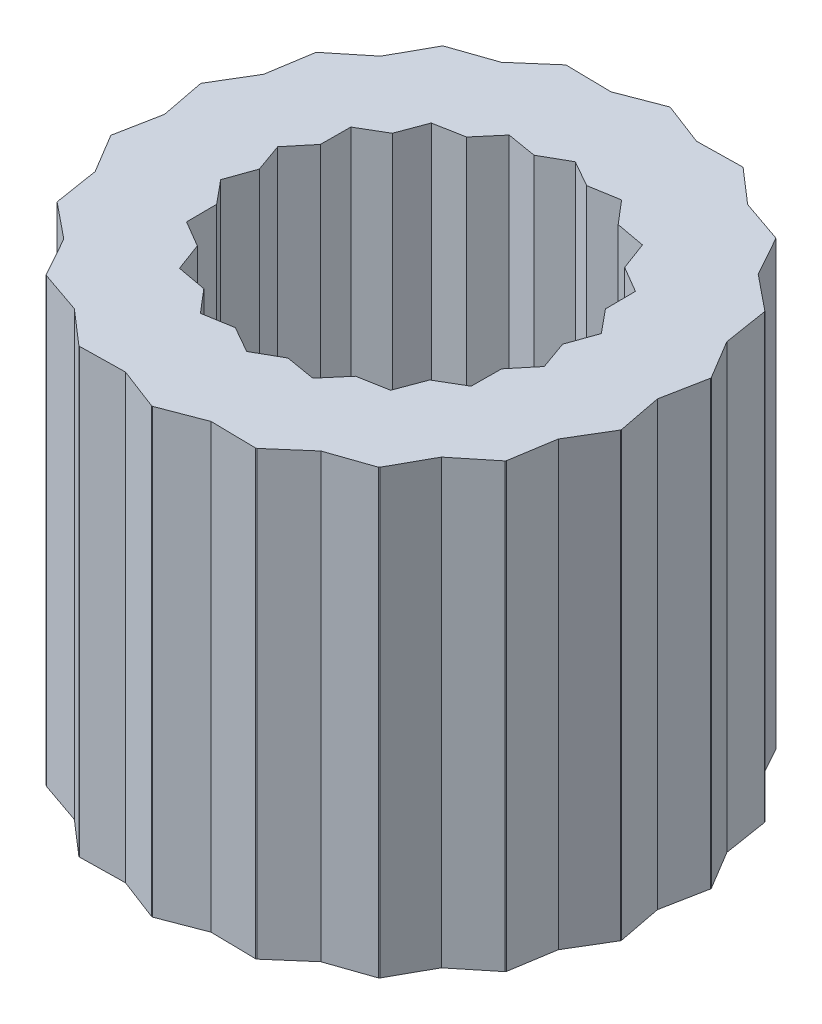
SolidWorks part; units mm, degrees
ref_plane "Front Plane" through (0, 0, 0) normal (0, 0, 1) x (1, 0, 0)
ref_plane "Top Plane" through (0, 0, 0) normal (0, 1, 0) x (1, 0, 0)
ref_plane "Right Plane" through (0, 0, 0) normal (1, 0, 0) x (0, 0, -1)
sketch "Sketch1" plane through (0, 0, 0) normal (0, 1, 0) x (1, 0, 0)
  line L0 (0, 0) -> (-0.8763, 4.97) construction
  line L1 (0, 0) -> (0.8632, 4.8954) construction
  line L2 (0, 0) -> (0, 4.9679) construction
  line L3 (0, 4.1) -> (-0.6772, 3.8408)
  line L4 (0, 4.1) -> (0.6772, 3.8408)
  line L5 (0, 2.6) -> (-0.4168, 2.3635)
  line L6 (0, 2.6) -> (0.4168, 2.3635)
  line L7 (1.4023, 3.8527) -> (0.6772, 3.8408)
  line L8 (1.4023, 3.8527) -> (1.95, 3.3775)
  line L9 (0.8893, 2.4432) -> (0.4168, 2.3635)
  line L10 (0.8893, 2.4432) -> (1.2, 2.0785)
  line L11 (2.6354, 3.1408) -> (1.95, 3.3775)
  line L12 (2.6354, 3.1408) -> (2.9876, 2.5069)
  line L13 (1.6712, 1.9917) -> (1.2, 2.0785)
  line L14 (1.6712, 1.9917) -> (1.8385, 1.5427)
  line L15 (3.5507, 2.05) -> (2.9876, 2.5069)
  line L16 (3.5507, 2.05) -> (3.6648, 1.3339)
  line L17 (2.2517, 1.3) -> (1.8385, 1.5427)
  line L18 (2.2517, 1.3) -> (2.2553, 0.8208)
  line L19 (4.0377, 0.712) -> (3.6648, 1.3339)
  line L20 (4.0377, 0.712) -> (3.9, 0)
  line L21 (2.5605, 0.4515) -> (2.2553, 0.8208)
  line L22 (2.5605, 0.4515) -> (2.4, 0)
  line L23 (4.0377, -0.712) -> (3.9, 0)
  line L24 (4.0377, -0.712) -> (3.6648, -1.3339)
  line L25 (2.5605, -0.4515) -> (2.4, 0)
  line L26 (2.5605, -0.4515) -> (2.2553, -0.8208)
  line L27 (3.5507, -2.05) -> (3.6648, -1.3339)
  line L28 (3.5507, -2.05) -> (2.9876, -2.5069)
  line L29 (2.2517, -1.3) -> (2.2553, -0.8208)
  line L30 (2.2517, -1.3) -> (1.8385, -1.5427)
  line L31 (2.6354, -3.1408) -> (2.9876, -2.5069)
  line L32 (2.6354, -3.1408) -> (1.95, -3.3775)
  line L33 (1.6712, -1.9917) -> (1.8385, -1.5427)
  line L34 (1.6712, -1.9917) -> (1.2, -2.0785)
  line L35 (1.4023, -3.8527) -> (1.95, -3.3775)
  line L36 (1.4023, -3.8527) -> (0.6772, -3.8408)
  line L37 (0.8893, -2.4432) -> (1.2, -2.0785)
  line L38 (0.8893, -2.4432) -> (0.4168, -2.3635)
  line L39 (0, -4.1) -> (0.6772, -3.8408)
  line L40 (0, -4.1) -> (-0.6772, -3.8408)
  line L41 (0, -2.6) -> (0.4168, -2.3635)
  line L42 (0, -2.6) -> (-0.4168, -2.3635)
  line L43 (-1.4023, -3.8527) -> (-0.6772, -3.8408)
  line L44 (-1.4023, -3.8527) -> (-1.95, -3.3775)
  line L45 (-0.8893, -2.4432) -> (-0.4168, -2.3635)
  line L46 (-0.8893, -2.4432) -> (-1.2, -2.0785)
  line L47 (-2.6354, -3.1408) -> (-1.95, -3.3775)
  line L48 (-2.6354, -3.1408) -> (-2.9876, -2.5069)
  line L49 (-1.6712, -1.9917) -> (-1.2, -2.0785)
  line L50 (-1.6712, -1.9917) -> (-1.8385, -1.5427)
  line L51 (-3.5507, -2.05) -> (-2.9876, -2.5069)
  line L52 (-3.5507, -2.05) -> (-3.6648, -1.3339)
  line L53 (-2.2517, -1.3) -> (-1.8385, -1.5427)
  line L54 (-2.2517, -1.3) -> (-2.2553, -0.8208)
  line L55 (-4.0377, -0.712) -> (-3.6648, -1.3339)
  line L56 (-4.0377, -0.712) -> (-3.9, 0)
  line L57 (-2.5605, -0.4515) -> (-2.2553, -0.8208)
  line L58 (-2.5605, -0.4515) -> (-2.4, 0)
  line L59 (-4.0377, 0.712) -> (-3.9, 0)
  line L60 (-4.0377, 0.712) -> (-3.6648, 1.3339)
  line L61 (-2.5605, 0.4515) -> (-2.4, 0)
  line L62 (-2.5605, 0.4515) -> (-2.2553, 0.8208)
  line L63 (-3.5507, 2.05) -> (-3.6648, 1.3339)
  line L64 (-3.5507, 2.05) -> (-2.9876, 2.5069)
  line L65 (-2.2517, 1.3) -> (-2.2553, 0.8208)
  line L66 (-2.2517, 1.3) -> (-1.8385, 1.5427)
  line L67 (-2.6354, 3.1408) -> (-2.9876, 2.5069)
  line L68 (-2.6354, 3.1408) -> (-1.95, 3.3775)
  line L69 (-1.6712, 1.9917) -> (-1.8385, 1.5427)
  line L70 (-1.6712, 1.9917) -> (-1.2, 2.0785)
  line L71 (-1.4023, 3.8527) -> (-1.95, 3.3775)
  line L72 (-1.4023, 3.8527) -> (-0.6772, 3.8408)
  line L73 (-0.8893, 2.4432) -> (-1.2, 2.0785)
  line L74 (-0.8893, 2.4432) -> (-0.4168, 2.3635)
  circle A0 centre (0, 0) radius 2.5 construction
  circle A1 centre (0, 0) radius 4 construction
  point P118 (0, 0)
  dimension "D1" = 5
  dimension "D2" = 8
  dimension "D3" = 10
  dimension "D4" = 10
  dimension "D5" = 4.1
  dimension "D6" = 3.9
  dimension "D7" = 2.4
  dimension "D8" = 2.6
  dimension "D9" = 18
extrude "Boss-Extrude1" add sketch "Sketch1" along normal blind 7 contours L72 L71 L68 L67 L64 L63 L60 L59 L56 L55 L52 L51 L48 L47 L44 L43 L40 L39 L36 L35 L32 L31 L28 L27 L24 L23 L20 L19 L16 L15 L12 L11 L8 L7 L4 L3 L73 L74 L5 L6 L9 L10 L13 L14 L17 L18 L21 L22 L25 L26
sketch "Sketch2" plane through (0, 7, 0) normal (0, 1, 0) x (1, 0, 0)
  circle A0 centre (0, 0) radius 4.097
  circle A1 centre (0, 0) radius 5.5151
extrude "Cut-Extrude1" cut sketch "Sketch2" against normal blind 10
